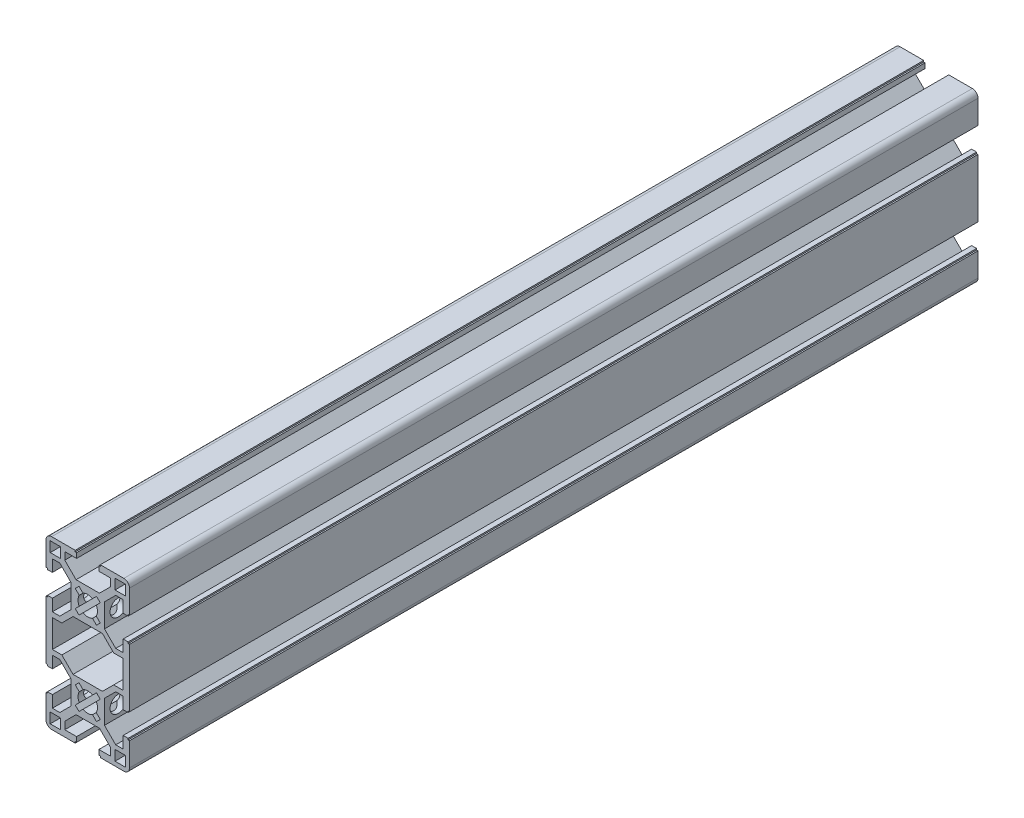
SolidWorks part; units mm, degrees
material "3003 Alloy"
ref_plane "Front Plane" through (0, 0, 0) normal (0, 0, 1) x (1, 0, 0)
ref_plane "Top Plane" through (0, 0, 0) normal (0, 1, 0) x (1, 0, 0)
ref_plane "Right Plane" through (0, 0, 0) normal (1, 0, 0) x (0, 0, -1)
sketch "Sketch2" plane through (0, 0, 0) normal (0, 0, 1) x (1, 0, 0)
  line L0 (-6, 10.7961) -> (-6, 15)
  line L1 (-6, 15) -> (-6, 19.2039)
  line L2 (-4.2039, 21) -> (0, 21)
  line L3 (0, 21) -> (4.2039, 21)
  line L4 (-13.476, -28.476) -> (-9.793, -28.476)
  line L5 (-9.793, -28.476) -> (-9.793, -24.793)
  line L6 (-9.793, -24.793) -> (-13.476, -24.793)
  line L7 (-13.476, -24.793) -> (-13.476, -28.476)
  line L8 (6, 19.2039) -> (6, 15)
  line L9 (-14.5, 11) -> (-12.714, 11)
  line L10 (-14.5, 10.5) -> (-14.5, 11)
  line L11 (-15, 10.5) -> (-14.5, 10.5)
  line L12 (-12.714, 11) -> (-12.714, 6.75)
  line L13 (-14.5, 19.5) -> (-15, 19.5)
  line L14 (-14.5, 19) -> (-14.5, 19.5)
  line L15 (-12.714, 19) -> (-14.5, 19)
  line L16 (-12.714, 23.25) -> (-12.714, 19)
  line L17 (-15, 19.5) -> (-15, 27.968)
  line L18 (-3.1431, 10.5099) -> (-4.4901, 11.8569)
  line L19 (-10.0461, 6.75) -> (-6, 10.7961)
  line L20 (-5.2816, 9) -> (-9.3096, 4.972)
  line L21 (-1.7079, 11.945) -> (-3.1431, 10.5099)
  line L22 (5.2816, 9) -> (-5.2816, 9)
  line L23 (-3.055, 16.7079) -> (-4.4901, 18.1431)
  line L24 (-6, 19.2039) -> (-10.0461, 23.25)
  line L25 (-4.4901, 18.1431) -> (-3.1431, 19.4901)
  line L26 (6, 15) -> (6, 10.7961)
  line L27 (-3.1431, 19.4901) -> (-1.7079, 18.055)
  line L28 (-6, -10.7961) -> (-6, -15)
  line L29 (-8.25, 27.714) -> (-8.25, 25.0461)
  line L30 (-4, 27.714) -> (-8.25, 27.714)
  line L31 (-4, 29.5) -> (-4, 27.714)
  line L32 (-4.5, 29.5) -> (-4, 29.5)
  line L33 (-4.5, 30) -> (-4.5, 29.5)
  line L34 (-8.25, 25.0461) -> (-4.2039, 21)
  line L35 (-4.4901, 11.8569) -> (-3.055, 13.2921)
  line L36 (-12.714, 6.75) -> (-10.0461, 6.75)
  line L37 (-12.968, 30) -> (-4.5, 30)
  line L38 (-10.0461, 23.25) -> (-12.714, 23.25)
  line L39 (-12.714, 4.972) -> (-9.3096, 4.972)
  line L40 (-13.476, 24.793) -> (-13.476, 28.476)
  line L41 (-9.793, 24.793) -> (-13.476, 24.793)
  line L42 (-9.793, 28.476) -> (-9.793, 24.793)
  line L43 (-13.476, 28.476) -> (-9.793, 28.476)
  line L44 (-6, -15) -> (-6, -19.2039)
  line L45 (-4.2039, -21) -> (0, -21)
  line L46 (14.5, -11) -> (12.714, -11)
  line L47 (14.5, -10.5) -> (14.5, -11)
  line L48 (15, -10.5) -> (14.5, -10.5)
  line L49 (12.714, -11) -> (12.714, -6.75)
  line L50 (15, 10.5) -> (15, -10.5)
  line L51 (12.714, 4.972) -> (12.714, -4.972)
  line L52 (14.5, -19.5) -> (15, -19.5)
  line L53 (14.5, -19) -> (14.5, -19.5)
  line L54 (12.714, -19) -> (14.5, -19)
  line L55 (12.714, -23.25) -> (12.714, -19)
  line L56 (15, -19.5) -> (15, -27.968)
  line L57 (3.1431, -10.5099) -> (4.4901, -11.8569)
  line L58 (10.0461, -6.75) -> (6, -10.7961)
  line L59 (5.2816, -9) -> (9.3096, -4.972)
  line L60 (1.7079, -11.945) -> (3.1431, -10.5099)
  line L61 (3.055, -16.7079) -> (4.4901, -18.1431)
  line L62 (6, -19.2039) -> (10.0461, -23.25)
  line L63 (4.4901, -18.1431) -> (3.1431, -19.4901)
  line L64 (0, -21) -> (4.2039, -21)
  line L65 (3.1431, -19.4901) -> (1.7079, -18.055)
  line L66 (8.25, -27.714) -> (8.25, -25.0461)
  line L67 (4, -27.714) -> (8.25, -27.714)
  line L68 (4, -29.5) -> (4, -27.714)
  line L69 (4.5, -29.5) -> (4, -29.5)
  line L70 (4.5, -30) -> (4.5, -29.5)
  line L71 (8.25, -25.0461) -> (4.2039, -21)
  line L72 (4.4901, -11.8569) -> (3.055, -13.2921)
  line L73 (12.714, -6.75) -> (10.0461, -6.75)
  line L74 (12.968, -30) -> (4.5, -30)
  line L75 (10.0461, -23.25) -> (12.714, -23.25)
  line L76 (12.714, -4.972) -> (9.3096, -4.972)
  line L77 (13.476, 28.476) -> (9.793, 28.476)
  line L78 (9.793, 28.476) -> (9.793, 24.793)
  line L79 (9.793, 24.793) -> (13.476, 24.793)
  line L80 (13.476, 24.793) -> (13.476, 28.476)
  line L81 (12.714, 4.972) -> (9.3096, 4.972)
  line L82 (10.0461, 23.25) -> (12.714, 23.25)
  line L83 (12.968, 30) -> (4.5, 30)
  line L84 (12.714, 6.75) -> (10.0461, 6.75)
  line L85 (4.4901, 11.8569) -> (3.055, 13.2921)
  line L86 (8.25, 25.0461) -> (4.2039, 21)
  line L87 (4.5, 30) -> (4.5, 29.5)
  line L88 (4.5, 29.5) -> (4, 29.5)
  line L89 (4, 29.5) -> (4, 27.714)
  line L90 (4, 27.714) -> (8.25, 27.714)
  line L91 (8.25, 27.714) -> (8.25, 25.0461)
  line L92 (3.1431, 19.4901) -> (1.7079, 18.055)
  line L93 (6, -19.2039) -> (6, -15)
  line L94 (4.4901, 18.1431) -> (3.1431, 19.4901)
  line L95 (6, 19.2039) -> (10.0461, 23.25)
  line L96 (3.055, 16.7079) -> (4.4901, 18.1431)
  line L97 (1.7079, 11.945) -> (3.1431, 10.5099)
  line L98 (5.2816, 9) -> (9.3096, 4.972)
  line L99 (10.0461, 6.75) -> (6, 10.7961)
  line L100 (3.1431, 10.5099) -> (4.4901, 11.8569)
  line L101 (15, 19.5) -> (15, 27.968)
  line L102 (12.714, 23.25) -> (12.714, 19)
  line L103 (12.714, 19) -> (14.5, 19)
  line L104 (14.5, 19) -> (14.5, 19.5)
  line L105 (14.5, 19.5) -> (15, 19.5)
  line L106 (12.714, 11) -> (12.714, 6.75)
  line L107 (15, 10.5) -> (14.5, 10.5)
  line L108 (14.5, 10.5) -> (14.5, 11)
  line L109 (14.5, 11) -> (12.714, 11)
  line L110 (13.476, -24.793) -> (13.476, -28.476)
  line L111 (9.793, -24.793) -> (13.476, -24.793)
  line L112 (9.793, -28.476) -> (9.793, -24.793)
  line L113 (13.476, -28.476) -> (9.793, -28.476)
  line L114 (-12.714, -4.972) -> (-9.3096, -4.972)
  line L115 (-10.0461, -23.25) -> (-12.714, -23.25)
  line L116 (-12.968, -30) -> (-4.5, -30)
  line L117 (-12.714, -6.75) -> (-10.0461, -6.75)
  line L118 (-4.4901, -11.8569) -> (-3.055, -13.2921)
  line L119 (-8.25, -25.0461) -> (-4.2039, -21)
  line L120 (-4.5, -30) -> (-4.5, -29.5)
  line L121 (-4.5, -29.5) -> (-4, -29.5)
  line L122 (-4, -29.5) -> (-4, -27.714)
  line L123 (-4, -27.714) -> (-8.25, -27.714)
  line L124 (-8.25, -27.714) -> (-8.25, -25.0461)
  line L125 (6, -15) -> (6, -10.7961)
  line L126 (-3.1431, -19.4901) -> (-1.7079, -18.055)
  line L128 (-4.4901, -18.1431) -> (-3.1431, -19.4901)
  line L129 (-6, -19.2039) -> (-10.0461, -23.25)
  line L130 (-3.055, -16.7079) -> (-4.4901, -18.1431)
  line L131 (5.2816, -9) -> (-5.2816, -9)
  line L132 (-1.7079, -11.945) -> (-3.1431, -10.5099)
  line L133 (-5.2816, -9) -> (-9.3096, -4.972)
  line L134 (-10.0461, -6.75) -> (-6, -10.7961)
  line L135 (-3.1431, -10.5099) -> (-4.4901, -11.8569)
  line L136 (-15, -19.5) -> (-15, -27.968)
  line L137 (-12.714, -23.25) -> (-12.714, -19)
  line L138 (-12.714, -19) -> (-14.5, -19)
  line L139 (-14.5, -19) -> (-14.5, -19.5)
  line L140 (-14.5, -19.5) -> (-15, -19.5)
  line L141 (-12.714, 4.972) -> (-12.714, -4.972)
  line L142 (-15, 10.5) -> (-15, -10.5)
  line L143 (-12.714, -11) -> (-12.714, -6.75)
  line L144 (-15, -10.5) -> (-14.5, -10.5)
  line L145 (-14.5, -10.5) -> (-14.5, -11)
  line L146 (-14.5, -11) -> (-12.714, -11)
  arc A0 (-15, 27.968) -> (-12.968, 30) centre (-12.968, 27.968) cw
  arc A1 (1.7079, 11.945) -> (-1.7079, 11.945) centre (0, 15) cw
  arc A2 (-3.055, 13.2921) -> (-3.055, 16.7079) centre (0, 15) cw
  arc A3 (-1.7079, 18.055) -> (1.7079, 18.055) centre (0, 15) cw
  arc A4 (15, -27.968) -> (12.968, -30) centre (12.968, -27.968) cw
  arc A5 (3.055, -13.2921) -> (3.055, -16.7079) centre (0, -15) cw
  arc A6 (3.055, 13.2921) -> (3.055, 16.7079) centre (0, 15) ccw
  arc A7 (15, 27.968) -> (12.968, 30) centre (12.968, 27.968) ccw
  arc A8 (-1.7079, -18.055) -> (1.7079, -18.055) centre (0, -15) ccw
  arc A9 (-3.055, -13.2921) -> (-3.055, -16.7079) centre (0, -15) ccw
  arc A10 (1.7079, -11.945) -> (-1.7079, -11.945) centre (0, -15) ccw
  arc A11 (-15, -27.968) -> (-12.968, -30) centre (-12.968, -27.968) ccw
  point P1 (-15, 30)
  point P3 (0, 30)
  point P4 (15, 30)
  point P5 (15, 15)
  point P15 (15, 0)
  point P16 (15, -15)
  point P17 (0, 0)
  point P32 (15, -30)
  point P53 (0, -30)
  point P54 (-15, -30)
  point P62 (-15, -15)
  point P63 (-15, 0)
  point P93 (-15, 15)
extrude "Boss-Extrude1" add sketch "Sketch2" along normal blind 304.8
sketch "Sketch4" plane through (-6, 0, 0) normal (-1, 0, 0) x (0, 0, 1)
  circle A0 centre (299.8, 15) radius 3
  circle A1 centre (299.8, -15) radius 3
extrude "Cut-Extrude2" cut sketch "Sketch4" against normal up to surface (21 mm away) up to face at (15, 0, 152.4)
sketch "Sketch6" plane through (0, -21, 0) normal (0, -1, 0) x (1, 0, 0)
  circle A0 centre (0, 7.5) radius 2
extrude "Cut-Extrude3" cut sketch "Sketch6" against normal up to surface (42 mm away) up to face at (0, 21, 152.4)
